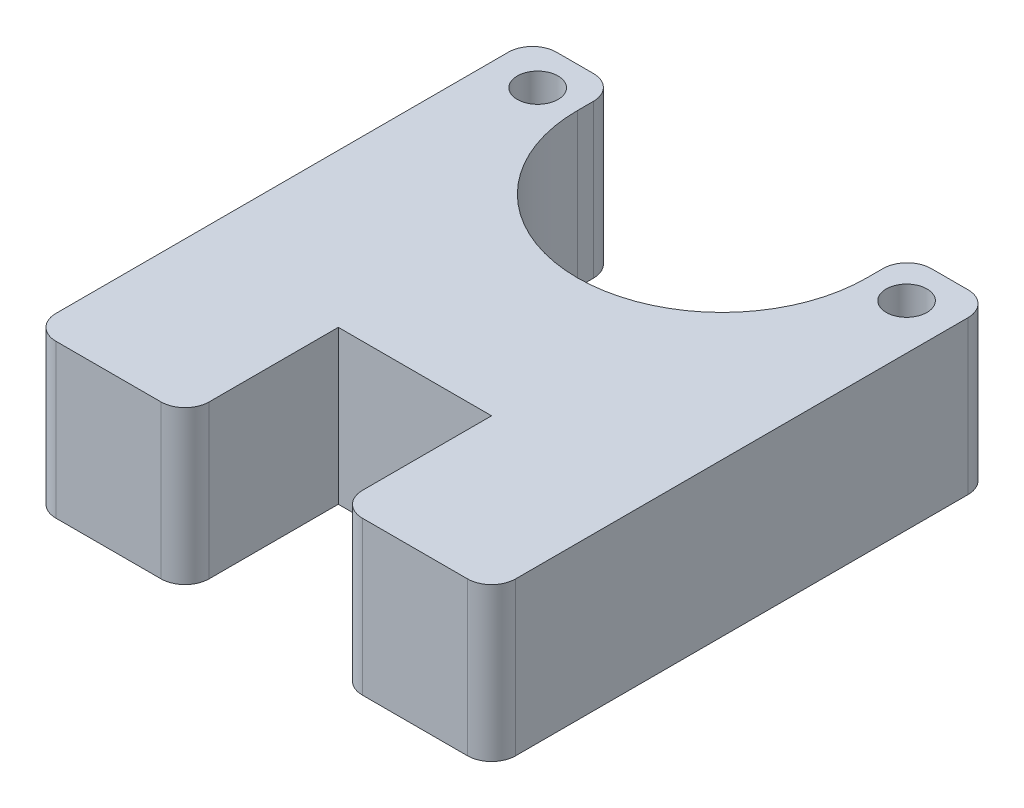
SolidWorks part; units mm, degrees
ref_plane "Front Plane" through (0, 0, 0) normal (0, 0, 1) x (1, 0, 0)
ref_plane "Top Plane" through (0, 0, 0) normal (0, 1, 0) x (1, 0, 0)
ref_plane "Right Plane" through (0, 0, 0) normal (1, 0, 0) x (0, 0, -1)
sketch "Sketch1" plane through (0, 0, 0) normal (0, 1, 0) x (1, 0, 0)
  line L0 (0, 0) -> (0, 6.0001)
  line L1 (0, 0) -> (19.05, 0)
  line L2 (0, 6.0001) -> (19.05, 6.0001)
  line L3 (19.05, 0) -> (19.05, 6.0001)
  line L4 (0, 6.0001) -> (0, 14.3937)
  line L5 (0, 6.0001) -> (3.525, 6.0001)
  line L6 (0, 14.3937) -> (3.525, 14.3937)
  line L7 (3.525, 6.0001) -> (3.525, 14.3937)
  line L8 (19.05, 6.0001) -> (19.05, 14.3937)
  line L9 (19.05, 6.0001) -> (15.525, 6.0001)
  line L10 (19.05, 14.3937) -> (15.525, 14.3937)
  line L11 (15.525, 6.0001) -> (15.525, 14.3937)
  line L12 (0, 0) -> (6.35, 0)
  line L13 (0, 0) -> (0, -6.35)
  line L14 (6.35, 0) -> (6.35, -6.35)
  line L15 (0, -6.35) -> (6.35, -6.35)
  line L16 (19.05, 0) -> (12.7, 0)
  line L17 (19.05, 0) -> (19.05, -6.35)
  line L18 (12.7, 0) -> (12.7, -6.35)
  line L19 (19.05, -6.35) -> (12.7, -6.35)
  arc A0 (3.525, 12.7287) -> (15.525, 12.7287) centre (9.525, 12.7287) ccw
  circle A1 centre (17.1675, 12.7287) radius 0.845
  circle A2 centre (1.8825, 12.7287) radius 0.845
  point P8 (9.525, 6.0001)
  dimension "D6" = 1.69
  dimension "D1" = 6.0001
  dimension "D2" = 6.35
  dimension "D3" = 6.7286
  dimension "D4" = 6
  dimension "D5" = 1.665
  dimension "D7" = 1.6425
  dimension "D9" = 6.35
  dimension "D10" = 6.35
  dimension "D11" = 6.35
  dimension "D12" = 6.35
  dimension "D13" = 1.6425
extrude "Boss-Extrude1" add sketch "Sketch1" along normal blind 6.35 contours L2 L7 L6 L4 A2 | A0 L7 L2 L11 | L11 L2 L8 L10 A1 | L1 L3 L2 L0 | L13 L15 L14 L1 | L19 L17 L1 L18
fillet "Fillet3" radius 1 8 edges at (19.05, 3.175, 6.35) (12.7, 3.175, 6.35) (6.35, 3.175, 6.35) (0, 3.175, 6.35) (19.05, 3.175, -14.3937) (15.525, 3.175, -14.3937) (3.525, 3.175, -14.3937) (0, 3.175, -14.3937)
equation "\"vigorwidth\"= 0.472441in"
equation "\"vigorflangewidth\"= 0.731102in"
equation "\"vigorflangelength\"= 0.131102in"
equation "\"vigorscrewsize\"= 0.066535in"
equation "\"vigorholeoffsetwid\"= 0.0646653in"
equation "\"vigorholeoffsetlen\"= 0.065551in"
equation "\"vigorflangedepth\"= 0.0901575in"
equation "\"vigordiscdepth\"= 0.0492126in"
equation "\"vigormotordepth\"= 1.12362in"
equation "\"vigortipdepth\"= 0.259055in"
equation "\"vigoraxlewidth\"= 0.173622in"
equation "\"vigorcutlen\"= 0.0480315in"
equation "\"vigoraxledepth\"= 0.159055in"
equation "\"D4@Sketch1\"=\"vigorwidth\"/2"
equation "\"rackoffset\"=.236224in"
equation "\"D1@Sketch1\"=\"rackoffset\""
equation "\"Slot\"=.25in"
equation "\"D10@Sketch1\"=\"Slot\""
equation "\"D9@Sketch1\"=\"Slot\""
equation "\"MotorMountLegLength\"=.25in"
equation "\"D11@Sketch1\"=\"MotorMountLegLength\""
equation "\"D12@Sketch1\"=\"MotorMountLegLength\""
equation "\"GearOffset\"=.264907in"
equation "\"D3@Sketch1\"=\"GearOffset\""
equation "\"D7@Sketch1\"=\"vigorholeoffsetwid\""
equation "\"D13@Sketch1\"=\"vigorholeoffsetwid\""
equation "\"D5@Sketch1\"=\"vigorflangelength\"/2"
equation "\"SlotSpacing\"=.25in"
equation "\"D2@Sketch1\"=\"SlotSpacing\""
equation "\"D6@Sketch1\"=\"vigorscrewsize\""
